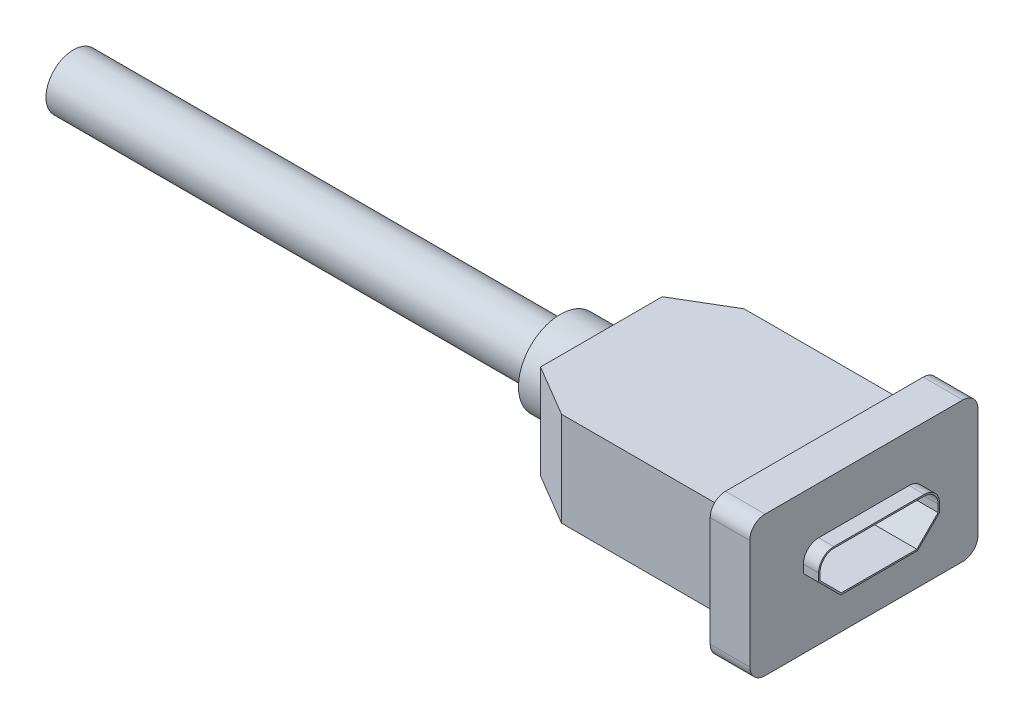
SolidWorks part; units mm, degrees
ref_plane "Front Plane" through (0, 0, 0) normal (0, 0, 1) x (1, 0, 0)
ref_plane "Top Plane" through (0, 0, 0) normal (0, 1, 0) x (1, 0, 0)
ref_plane "Right Plane" through (0, 0, 0) normal (1, 0, 0) x (0, 0, -1)
sketch "Sketch1" plane through (0, 0, 0) normal (0, 1, 0) x (1, 0, 0)
  line L0 (0, 6) -> (0, -6)
  line L1 (0, -6) -> (-13.87, -6)
  line L2 (-13.87, -6) -> (-17.25, -4)
  line L3 (-17.25, -4) -> (-17.25, 4)
  line L4 (-17.25, 4) -> (-13.87, 6)
  line L5 (-13.87, 6) -> (0, 6)
  point P3 (0, 0)
  point P8 (-17.25, 0)
  point P9 (0, 0)
  point P10 (-15.5971, 2.4319)
  dimension "D1" = 13.87
  dimension "D2" = 12
  dimension "D3" = 17.25
  dimension "D4" = 8
extrude "Boss-Extrude1" add sketch "Sketch1" along normal mid plane 6.2
sketch "Sketch2" plane through (0, 0, 0) normal (1, 0, 0) x (0, 0, -1)
  line L8 (-7.5, -4.6) -> (7.5, -4.6)
  line L9 (7.5, -4.6) -> (7.5, 4.6)
  line L10 (7.5, 4.6) -> (-7.5, 4.6)
  line L11 (-7.5, 4.6) -> (-7.5, -4.6)
  line L12 (-7.5, -4.6) -> (7.5, -4.6)
  line L13 (7.5, -4.6) -> (7.5, 4.6)
  line L14 (7.5, 4.6) -> (-7.5, 4.6)
  line L15 (-7.5, 4.6) -> (-7.5, -4.6)
  dimension "D1" = 1.5
extrude "Boss-Extrude2" add sketch "Sketch2" against normal blind 2.6
sketch "Sketch3" plane through (-17.25, 0, 0) normal (-1, 0, 0) x (0, 0, 1)
  circle A0 centre (0, 0) radius 2.75
  dimension "D1" = 5.5
extrude "Boss-Extrude3" add sketch "Sketch3" along normal blind 2.7
sketch "Sketch4" plane through (-19.95, 0, 0) normal (-1, 0, 0) x (0, 0, 1)
  circle A0 centre (0, 0) radius 1.8
  dimension "D1" = 3.6
extrude "Boss-Extrude4" add sketch "Sketch4" along normal blind 32
fillet "Fillet1" radius 1 4 edges at (-1.3, 4.6, 7.5) (-1.3, -4.6, 7.5) (-1.3, -4.6, -7.5) (-1.3, 4.6, -7.5)
sketch "Sketch5" plane through (0, 0, 0) normal (1, 0, 0) x (0, 0, -1)
  line L0 (2.975, 1.39) -> (-2.975, 1.39)
  line L1 (-3.875, -1.39) -> (3.875, -1.39) construction
  line L2 (-3.875, -1.39) -> (-3.875, 1.39) construction
  line L3 (-3.875, 1.39) -> (3.875, 1.39) construction
  line L4 (3.875, -1.39) -> (3.875, 1.39) construction
  line L5 (-3.875, -1.39) -> (3.875, 1.39) construction
  line L6 (-3.875, 1.39) -> (3.875, -1.39) construction
  line L7 (-3.875, 0.49) -> (-3.875, 0)
  line L8 (-3.875, 0) -> (-2.485, -1.39)
  line L9 (-2.485, -1.39) -> (2.485, -1.39)
  line L11 (0, 5.06) -> (0, -5.06) construction
  line L12 (3.875, 0) -> (2.485, -1.39)
  line L13 (3.875, 0.49) -> (3.875, 0)
  arc A0 (-2.975, 1.39) -> (-3.875, 0.49) centre (-2.975, 0.49) ccw
  arc A1 (2.975, 1.39) -> (3.875, 0.49) centre (2.975, 0.49) cw
  point P0 (0, 0)
  point P10 (0, 0)
  dimension "D3" = 0.9
  dimension "D1" = 2.78
  dimension "D2" = 7.75
  dimension "D4" = 45
extrude "Cut-Extrude1" cut sketch "Sketch5" against normal blind 7
sketch "Sketch7" plane through (0, 0, 0) normal (1, 0, 0) x (0, 0, -1)
  line L0 (2.975, 1.49) -> (-2.975, 1.49)
  line L1 (-3.975, 0.49) -> (-3.975, -0.0414)
  line L2 (-3.975, -0.0414) -> (-2.5264, -1.49)
  line L3 (-2.5264, -1.49) -> (2.5264, -1.49)
  line L4 (2.5264, -1.49) -> (3.975, -0.0414)
  line L5 (3.975, -0.0414) -> (3.975, 0.49)
  line L6 (-3.875, 0.49) -> (-3.875, 0)
  line L7 (-3.875, 0) -> (-2.485, -1.39)
  line L8 (-2.485, -1.39) -> (2.485, -1.39)
  line L9 (2.485, -1.39) -> (3.875, 0)
  line L10 (3.875, 0) -> (3.875, 0.49)
  line L11 (2.975, 1.39) -> (-2.975, 1.39)
  line L12 (-3.875, 0.49) -> (-3.875, 0)
  line L13 (-3.875, 0) -> (-2.485, -1.39)
  line L14 (-2.485, -1.39) -> (2.485, -1.39)
  line L15 (2.485, -1.39) -> (3.875, 0)
  line L16 (3.875, 0) -> (3.875, 0.49)
  line L17 (2.975, 1.39) -> (-2.975, 1.39)
  arc A0 (-2.975, 1.49) -> (-3.975, 0.49) centre (-2.975, 0.49) ccw
  arc A1 (3.975, 0.49) -> (2.975, 1.49) centre (2.975, 0.49) ccw
  arc A2 (-2.975, 1.39) -> (-3.875, 0.49) centre (-2.975, 0.49) ccw
  arc A3 (3.875, 0.49) -> (2.975, 1.39) centre (2.975, 0.49) ccw
  arc A4 (-2.975, 1.39) -> (-3.875, 0.49) centre (-2.975, 0.49) ccw
  arc A5 (3.875, 0.49) -> (2.975, 1.39) centre (2.975, 0.49) ccw
  dimension "D1" = 0
  dimension "D2" = 0.1
extrude "Boss-Extrude5" add sketch "Sketch7" along normal blind 1
